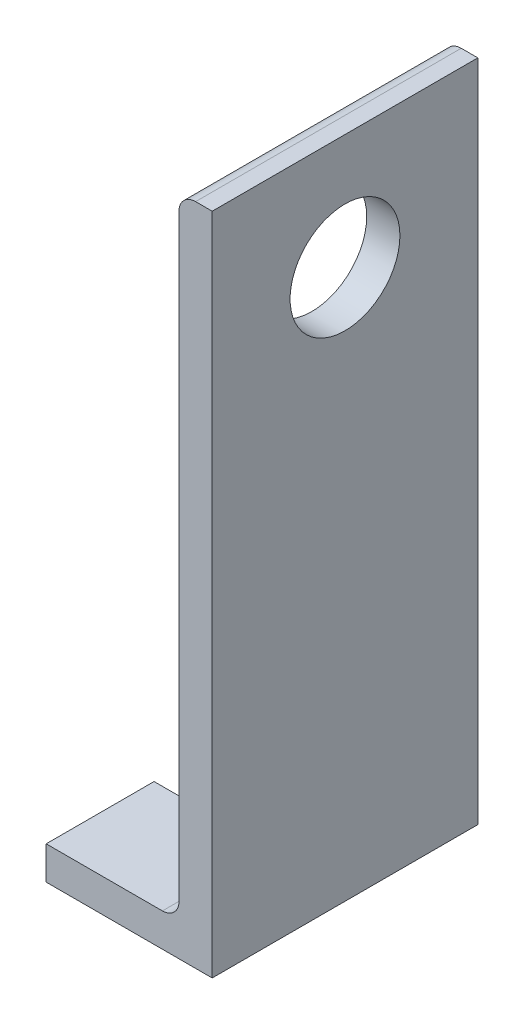
SolidWorks part; units mm, degrees
ref_plane "Front Plane" through (0, 0, 0) normal (0, 0, 1) x (1, 0, 0)
ref_plane "Top Plane" through (0, 0, 0) normal (0, 1, 0) x (1, 0, 0)
ref_plane "Right Plane" through (0, 0, 0) normal (1, 0, 0) x (0, 0, -1)
sketch "Sketch2" plane through (0, 0, 0) normal (0, 0, 1) x (1, 0, 0)
  line L0 (-15.875, 0) -> (15.875, 0)
  line L1 (15.875, 0) -> (15.875, 127)
  line L2 (15.875, 127) -> (9.525, 127) construction
  line L3 (9.525, 123.825) -> (9.525, 9.525)
  line L4 (6.35, 6.35) -> (-12.7, 6.35)
  line L5 (-15.875, 0) -> (-15.875, 6.35) construction
  line L6 (12.7, 127) -> (15.875, 127)
  line L7 (-15.875, 3.175) -> (-15.875, 0)
  line L8 (-12.7, 6.35) -> (-15.875, 6.35)
  line L9 (-15.875, 6.35) -> (-15.875, 3.175)
  arc A0 (9.525, 123.825) -> (12.7, 127) centre (12.7, 123.825) cw
  arc A2 (9.525, 9.525) -> (6.35, 6.35) centre (6.35, 9.525) cw
  dimension "Vert" = 127
  dimension "Horz" = 31.75
  dimension "Thickness" = 6.35
extrude "Boss-Extrude1" add sketch "Sketch2" along normal mid plane 50.8
ref_plane "Contact Plane 1" through (0, 6.35, 0) normal (0, 1, 0) x (1, 0, 0)
ref_plane "Contact Plane 2" through (9.525, 0, 0) normal (-1, 0, 0) x (0, 0, 1)
sketch "Sketch3" plane through (0, 0, 0) normal (0, -1, 0) x (1, 0, 0)
  line L0 (15.875, 0) -> (-15.875, 0) construction
  line L1 (15.875, 25.4) -> (15.875, -25.4) construction
  line L2 (-15.875, 25.4) -> (-15.875, -25.4) construction
  circle A0 centre (-4.826, 0) radius 4.765
  dimension "D1" = 9.53
  dimension "D2" = 20.701
extrude "Cut-Extrude1" cut sketch "Sketch3" against normal through all contours A0
sketch "Sketch5" plane through (15.875, 0, 0) normal (1, 0, 0) x (0, 0, -1)
  line L0 (-25.4, 0) -> (-25.4, 127) construction
  circle A0 centre (0, 105) radius 10.5
  dimension "D1" = 25.4
  dimension "D2" = 105
  dimension "D3" = 21
extrude "Cut-Extrude2" cut sketch "Sketch5" against normal blind 10
sketch "Sketch6" plane through (0, 0, 0) normal (0, -1, 0) x (1, 0, 0)
  line L0 (-4.826, 4.765) -> (-15.875, 4.765)
  line L1 (-15.875, 25.4) -> (-15.875, -25.4) construction
  line L2 (-4.826, -4.765) -> (-15.875, -4.765)
  line L3 (-15.875, -4.765) -> (-15.875, 4.765)
  line L4 (-4.826, 4.765) -> (-4.826, -4.765)
  circle A0 centre (-4.826, 0) radius 4.765 construction
extrude "Cut-Extrude3" cut sketch "Sketch6" against normal blind 10
